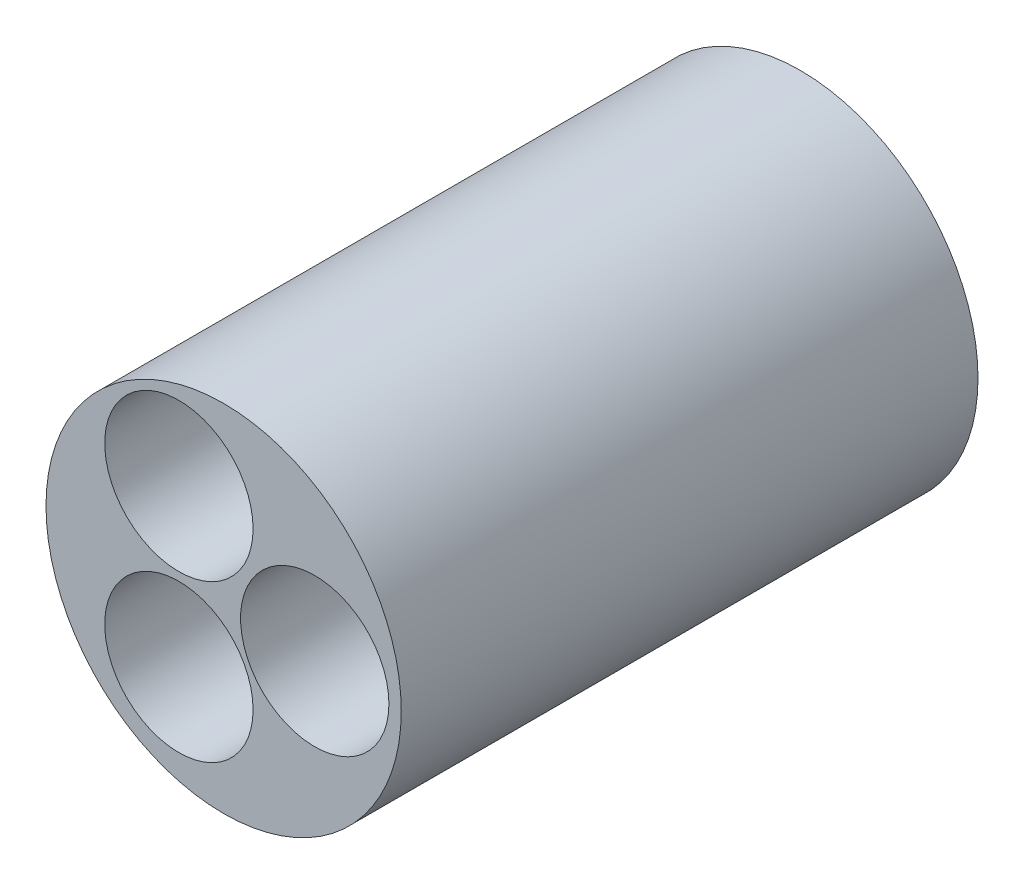
SolidWorks part; units mm, degrees
ref_plane "Front Plane" through (0, 0, 0) normal (0, 0, 1) x (1, 0, 0)
ref_plane "Top Plane" through (0, 0, 0) normal (0, 1, 0) x (1, 0, 0)
ref_plane "Right Plane" through (0, 0, 0) normal (1, 0, 0) x (0, 0, -1)
sketch "Sketch1" plane through (0, 0, 0) normal (0, 0, 1) x (1, 0, 0)
  line L0 (0, 19.05) -> (0, 0) construction
  circle A0 centre (0, 0) radius 9.017
  circle A1 centre (0, 19.05) radius 9.017
  circle A2 centre (16.51, 8.875) radius 9.017
  circle A3 centre (5.437, 8.875) radius 21.59
  point P7 (0, 9.525)
  dimension "D1" = 19.05
  dimension "D2" = 16.51
  dimension "D3" = 18.034
  dimension "D4" = 18.034
  dimension "D5" = 18.034
extrude "Boss-Extrude1" add sketch "Sketch1" along normal blind 70.1
